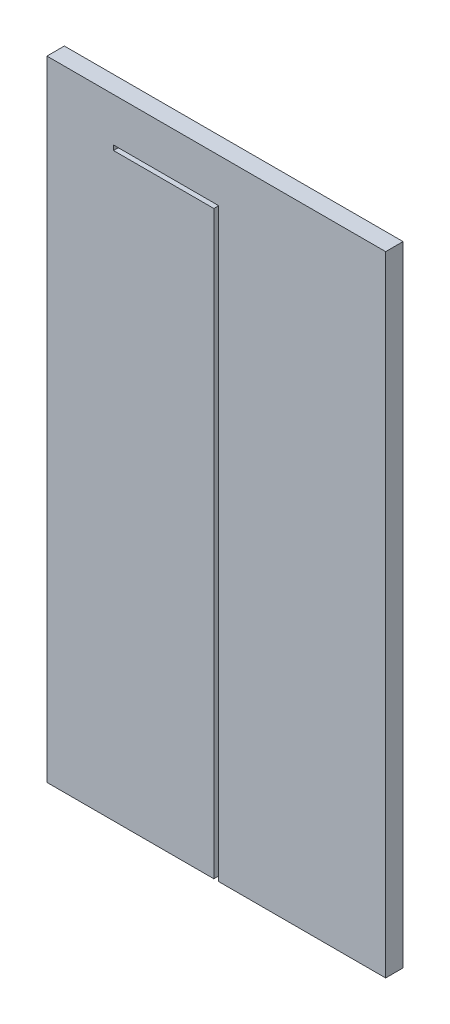
SolidWorks part; units mm, degrees
material "Balza"
ref_plane "Přední rovina" through (0, 0, 0) normal (0, 0, 1) x (1, 0, 0)
ref_plane "Horní rovina" through (0, 0, 0) normal (0, 1, 0) x (1, 0, 0)
ref_plane "Pravá rovina" through (0, 0, 0) normal (1, 0, 0) x (0, 0, -1)
sketch "Skica1" plane through (0, 0, 0) normal (0, 0, 1) x (1, 0, 0)
  line L1 (0, 0) -> (350, 0)
  line L2 (0, 0) -> (0, 650)
  line L3 (0, 650) -> (350, 650)
  line L4 (350, 0) -> (350, 650)
  dimension "D1" = 650
  dimension "D2" = 350
extrude "Přidat vysunutím2" add sketch "Skica1" along normal blind 18
sketch "profil na frezu" plane through (0, 0, 0) normal (0, -1, 0) x (1, 0, 0)
  line L0 (175, -982) -> (175, 49018) construction
  line L1 (0, 18) -> (350, 18) construction
  line L2 (190, 3) -> (190, 8)
  line L3 (190, 3) -> (160, 3)
  line L4 (160, 3) -> (160, 8)
  line L5 (160, 8) -> (172.5, 8)
  line L6 (172.5, 8) -> (172.5, 18)
  line L7 (172.5, 18) -> (177.5, 18)
  line L8 (190, 8) -> (177.5, 8)
  line L9 (177.5, 8) -> (177.5, 18)
  point P5 (175, 18)
  point P11 (0, 0)
  point P12 (175, 3)
  point P15 (175, 18)
  dimension "D1" = 30
  dimension "D2" = 15
  dimension "D3" = 5
  dimension "D4" = 5
sketch "cesta" plane through (0, 0, 18) normal (0, 0, 1) x (1, 0, 0)
  line L0 (175, 0) -> (175, 602.3572)
  line L1 (175, 602.3572) -> (68.7877, 602.3572)
  line L2 (175, 533.9842) -> (281.7299, 533.9842)
  line L3 (175, 406.4389) -> (68.7877, 406.4389)
  line L4 (175, 372.114) -> (281.7299, 372.114)
  line L5 (175, 181.3558) -> (36.8497, 181.3558)
  line L6 (36.8497, 181.3558) -> (36.8497, 47.2879)
  line L7 (175, 181.3558) -> (287.6731, 181.3558)
  line L8 (287.6731, 181.3558) -> (287.6731, 47.2879)
sweep "Odebrat tažením po křivce8" cut profiles "profil na frezu" path "cesta"
